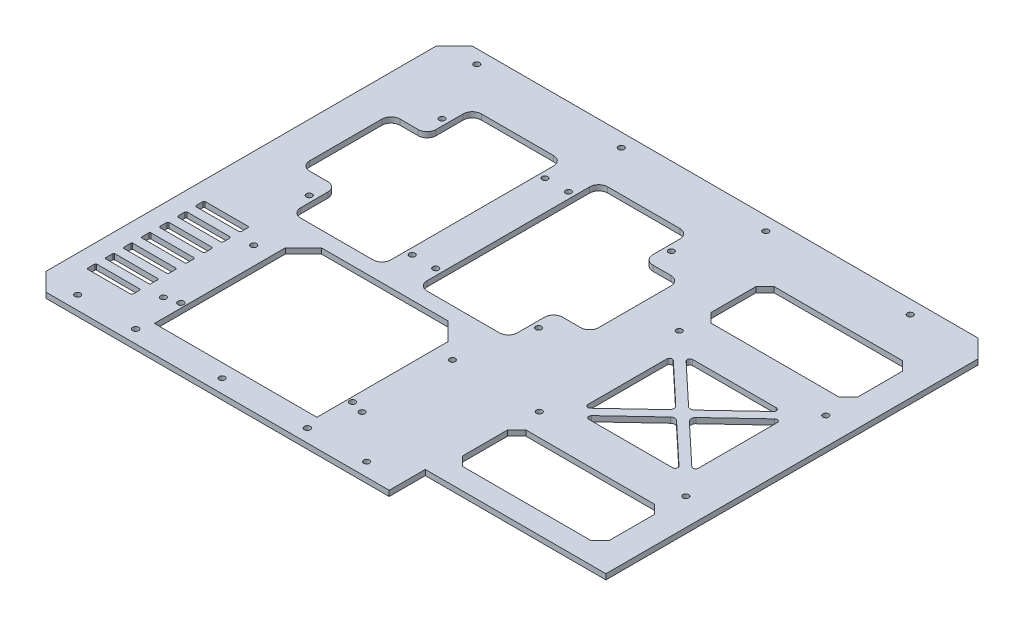
SolidWorks part; units mm, degrees
material "Thornel Mat VMA"
ref_plane "前视基准面" through (0, 0, 0) normal (0, 0, 1) x (1, 0, 0)
ref_plane "上视基准面" through (0, 0, 0) normal (0, 1, 0) x (1, 0, 0)
ref_plane "右视基准面" through (0, 0, 0) normal (1, 0, 0) x (0, 0, -1)
sketch "草图1" plane through (0, 0, 0) normal (0, 1, 0) x (1, 0, 0)
  line L0 (-100, -110.5) -> (100, -110.5) construction
  line L1 (-100, -118) -> (100, -118)
  line L2 (-100, -118) -> (-100, 118)
  line L3 (-100, 118) -> (100, 118)
  line L4 (100, -118) -> (100, 118)
  line L5 (-100, -118) -> (100, 118) construction
  line L6 (-100, 118) -> (100, -118) construction
  line L7 (0, 0) -> (61.3463, 0) construction
  line L8 (0, 0) -> (0, -52.9296) construction
  circle A0 centre (0, -110.5) radius 1.6
  circle A1 centre (-80, -110.5) radius 1.6
  circle A2 centre (80, -110.5) radius 1.6
  circle A3 centre (80, 110.5) radius 1.6
  circle A4 centre (0, 110.5) radius 1.6
  circle A5 centre (-80, 110.5) radius 1.6
  point P0 (0, 0)
  dimension "D4" = 3.2
  dimension "D6" = 3.2
  dimension "D1" = 200
  dimension "D2" = 236
  dimension "D3" = 7.5
  dimension "D5" = 80
extrude "凸台-拉伸1" add sketch "草图1" along normal blind 3
sketch "草图2" plane through (0, 3, 0) normal (0, 1, 0) x (1, 0, 0)
  line L0 (0, -110.5) -> (0, 110.5) construction
  line L1 (100, 118) -> (-100, 118) construction
  line L2 (6.5, 74.75) -> (63.5, 74.75) construction
  line L3 (6.5, 74.75) -> (6.5, 1.25) construction
  line L4 (6.5, 1.25) -> (63.5, 1.25) construction
  line L5 (63.5, 74.75) -> (63.5, 1.25) construction
  line L6 (6.5, 74.75) -> (63.5, 1.25) construction
  line L7 (6.5, 1.25) -> (63.5, 74.75) construction
  circle A0 centre (6.5, 74.75) radius 1.6
  circle A1 centre (63.5, 74.75) radius 1.6
  circle A2 centre (6.5, 1.25) radius 1.6
  circle A3 centre (63.5, 1.25) radius 1.6
  circle A4 centre (-6.5, 74.75) radius 1.6
  circle A5 centre (-63.5, 74.75) radius 1.6
  circle A6 centre (-63.5, 1.25) radius 1.6
  circle A7 centre (-6.5, 1.25) radius 1.6
  point P4 (35, 38)
  dimension "D5" = 3.2
  dimension "D6" = 3.2
  dimension "D7" = 3.2
  dimension "D8" = 3.2
  dimension "D1" = 73.5
  dimension "D2" = 57
  dimension "D3" = 35
  dimension "D4" = 80
extrude "切除-拉伸1" cut sketch "草图2" against normal up to next
sketch "草图3" plane through (0, 3, 0) normal (0, 1, 0) x (1, 0, 0)
  line L0 (-63.5, 1.25) -> (-6.5, 1.25) construction
  line L1 (-63.5, 74.75) -> (-6.5, 74.75) construction
  line L2 (-35, 74.75) -> (-35, 1.25) construction
  line L3 (0, 0) -> (0, 32.6506) construction
  line L4 (-60, -12) -> (-10, -12)
  line L5 (-60, -12) -> (-60, 88)
  line L6 (-60, 88) -> (-10, 88)
  line L7 (-10, -12) -> (-10, 88)
  line L8 (-60, -12) -> (-10, 88) construction
  line L9 (-60, 88) -> (-10, -12) construction
  line L10 (60, -12) -> (10, -12)
  line L11 (10, -12) -> (10, 88)
  line L12 (60, 88) -> (10, 88)
  line L13 (60, -12) -> (60, 88)
  point P10 (-35, 38)
  dimension "D1" = 50
  dimension "D2" = 100
extrude "切除-拉伸2" cut sketch "草图3" against normal up to next
sketch "草图4" plane through (0, 3, 0) normal (0, 1, 0) x (1, 0, 0)
  line L0 (-60, 38) -> (-70, 38) construction
  line L1 (-60, 88) -> (-60, -12) construction
  line L2 (0, 0) -> (0, 48.7718) construction
  line L3 (-80, 13) -> (-60, 13)
  line L4 (-80, 13) -> (-80, 63)
  line L5 (-80, 63) -> (-60, 63)
  line L6 (-60, 13) -> (-60, 63)
  line L7 (-80, 13) -> (-60, 63) construction
  line L8 (-80, 63) -> (-60, 13) construction
  line L9 (80, 13) -> (60, 13)
  line L10 (60, 13) -> (60, 63)
  line L11 (80, 63) -> (60, 63)
  line L12 (80, 13) -> (80, 63)
  dimension "D1" = 10
  dimension "D2" = 50
extrude "切除-拉伸3" cut sketch "草图4" against normal up to next
fillet "圆角1" radius 5 16 edges at (10, 1.5, 12) (60, 1.5, 12) (60, 1.5, -13) (80, 1.5, -13) (80, 1.5, -63) (60, 1.5, -63) (60, 1.5, -88) (10, 1.5, -88) (-60, 1.5, -13) (-80, 1.5, -13) (-80, 1.5, -63) (-60, 1.5, -63) (-10, 1.5, -88) (-60, 1.5, -88) (-10, 1.5, 12) (-60, 1.5, 12)
sketch "草图5" plane through (0, 3, 0) normal (0, 1, 0) x (1, 0, 0)
  line L0 (0, -110.5) -> (0, -65.5) construction
  line L2 (-25, -40.5) -> (25, -40.5) construction
  line L3 (-25, -40.5) -> (-25, -90.5) construction
  line L4 (-25, -90.5) -> (25, -90.5) construction
  line L5 (25, -40.5) -> (25, -90.5) construction
  line L6 (-25, -40.5) -> (25, -90.5) construction
  line L7 (-25, -90.5) -> (25, -40.5) construction
  circle A0 centre (25, -40.5) radius 1.6
  circle A1 centre (-25, -40.5) radius 1.6
  circle A2 centre (25, -90.5) radius 1.6
  circle A3 centre (-25, -90.5) radius 1.6
  dimension "D4" = 3.2
  dimension "D5" = 3.2
  dimension "D6" = 3.2
  dimension "D7" = 3.2
  dimension "D1" = 45
  dimension "D2" = 50
  dimension "D3" = 50
extrude "切除-拉伸4" cut sketch "草图5" against normal up to next
sketch "草图6" plane through (0, 3, 0) normal (0, 1, 0) x (1, 0, 0)
  line L0 (-25, -40.5) -> (0, -65.5) construction
  line L1 (-22.5, -52.5711) -> (-22.5, -78.4289)
  line L2 (-18.2322, -80.1967) -> (-5.3033, -67.2678)
  line L3 (-18.2322, -50.8033) -> (-5.3033, -63.7322)
  line L4 (-25, -40.5) -> (-25, -90.5) construction
  line L5 (-25, -90.5) -> (0, -65.5) construction
  line L6 (-22.5, -46.5355) -> (-3.5355, -65.5) construction
  line L7 (-22.5, -84.4645) -> (-3.5355, -65.5) construction
  line L8 (-22.5, -46.5355) -> (-22.5, -84.4645) construction
  line L9 (12.9289, -43) -> (-12.9289, -43)
  line L10 (14.6967, -47.2678) -> (1.7678, -60.1967)
  line L11 (-14.6967, -47.2678) -> (-1.7678, -60.1967)
  line L12 (22.5, -78.4289) -> (22.5, -52.5711)
  line L13 (18.2322, -80.1967) -> (5.3033, -67.2678)
  line L14 (18.2322, -50.8033) -> (5.3033, -63.7322)
  line L15 (-12.9289, -88) -> (12.9289, -88)
  line L16 (-14.6967, -83.7322) -> (-1.7678, -70.8033)
  line L17 (14.6967, -83.7322) -> (1.7678, -70.8033)
  arc A0 (-5.3033, -63.7322) -> (-5.3033, -67.2678) centre (-7.0711, -65.5) cw
  arc A1 (-18.2322, -80.1967) -> (-22.5, -78.4289) centre (-20, -78.4289) cw
  arc A2 (-18.2322, -50.8033) -> (-22.5, -52.5711) centre (-20, -52.5711) ccw
  arc A3 (-14.6967, -47.2678) -> (-12.9289, -43) centre (-12.9289, -45.5) cw
  arc A4 (14.6967, -47.2678) -> (12.9289, -43) centre (12.9289, -45.5) ccw
  arc A5 (1.7678, -60.1967) -> (-1.7678, -60.1967) centre (0, -58.4289) cw
  arc A6 (18.2322, -50.8033) -> (22.5, -52.5711) centre (20, -52.5711) cw
  arc A7 (18.2322, -80.1967) -> (22.5, -78.4289) centre (20, -78.4289) ccw
  arc A8 (5.3033, -67.2678) -> (5.3033, -63.7322) centre (7.0711, -65.5) cw
  arc A9 (14.6967, -83.7322) -> (12.9289, -88) centre (12.9289, -85.5) cw
  arc A10 (-14.6967, -83.7322) -> (-12.9289, -88) centre (-12.9289, -85.5) ccw
  arc A11 (-1.7678, -70.8033) -> (1.7678, -70.8033) centre (0, -72.5711) cw
  point P47 (0, -65.5)
  dimension "D2" = 2.5
  dimension "D1" = 2.5
  dimension "D3" = 4
extrude "切除-拉伸5" cut sketch "草图6" against normal up to next
sketch "草图7" plane through (0, 3, 0) normal (0, 1, 0) x (1, 0, 0)
  line L0 (-22.5, -65.5) -> (22.5, -65.5) construction
  line L1 (-22.5, -52.5711) -> (-22.5, -78.4289) construction
  line L2 (22.5, -78.4289) -> (22.5, -52.5711) construction
  line L3 (-100, -118) -> (100, -118) construction
  line L4 (-35, -28) -> (35, -28)
  line L5 (-35, -28) -> (-35, -103)
  line L6 (-35, -103) -> (35, -103)
  line L7 (35, -28) -> (35, -103)
  line L8 (-35, -28) -> (35, -103) construction
  line L9 (-35, -103) -> (35, -28) construction
  point P6 (0, -65.5)
  dimension "D1" = 70
  dimension "D2" = 15
extrude "切除-拉伸6" cut sketch "草图7" against normal up to next
sketch "草图8" plane through (0, 3, 0) normal (0, 1, 0) x (1, 0, 0)
  line L0 (35, -28) -> (-35, -28) construction
  line L1 (-35, -20.5) -> (35, -20.5)
  line L2 (-35, -20.5) -> (-35, -35.5)
  line L3 (-35, -35.5) -> (35, -35.5)
  line L4 (35, -20.5) -> (35, -35.5)
  line L5 (-35, -20.5) -> (35, -35.5) construction
  line L6 (-35, -35.5) -> (35, -20.5) construction
  line L7 (35, -103) -> (35, -28) construction
  point P0 (0, -28)
  dimension "D1" = 15
extrude "切除-拉伸7" cut sketch "草图8" against normal up to next
sketch "草图9" plane through (0, 3, 0) normal (0, 1, 0) x (1, 0, 0)
  line L0 (-35, -61.75) -> (35, -61.75) construction
  line L1 (-35, -20.5) -> (-35, -103) construction
  line L2 (35, -103) -> (35, -20.5) construction
  line L4 (-45, -20.5) -> (45, -20.5)
  line L5 (-45, -20.5) -> (-45, -103)
  line L6 (-45, -103) -> (45, -103)
  line L7 (45, -20.5) -> (45, -103)
  line L8 (-45, -20.5) -> (45, -103) construction
  line L9 (-45, -103) -> (45, -20.5) construction
  point P6 (0, -61.75)
  dimension "D1" = 82.5
  dimension "D2" = 90
extrude "切除-拉伸8" cut sketch "草图9" against normal up to next
chamfer "倒角2" distance 10 angle 45 2 edges at (45, 1.5, 20.5) (-45, 1.5, 20.5)
sketch "草图10" plane through (0, 3, 0) normal (0, 1, 0) x (1, 0, 0)
  line L0 (0, -118) -> (0, -88) construction
  line L1 (-100, -118) -> (100, -118) construction
  line L2 (-55, -88) -> (55, -88) construction
  line L3 (55, -88) -> (55, -38) construction
  circle A0 centre (55, -38) radius 1.6
  circle A1 centre (55, -88) radius 1.6
  circle A2 centre (-55, -88) radius 1.6
  circle A3 centre (-55, -38) radius 1.6
  dimension "D4" = 3.2
  dimension "D5" = 3.2
  dimension "D1" = 30
  dimension "D2" = 110
  dimension "D3" = 50
extrude "切除-拉伸9" cut sketch "草图10" against normal up to next
sketch "草图11" plane through (0, 3, 0) normal (0, 1, 0) x (1, 0, 0)
  line L0 (-55, -38) -> (-55, -88) construction
  line L1 (-55, -63) -> (-100, -63) construction
  line L2 (-100, 118) -> (-100, -118) construction
  line L3 (-89.5, -60.5) -> (-90, -61)
  line L4 (-89.5, -60.5) -> (-65.5, -60.5)
  line L5 (-90, -61) -> (-90, -65)
  line L6 (-89.5, -65.5) -> (-65.5, -65.5)
  line L7 (-65, -61) -> (-65, -65)
  line L8 (-90, -60.5) -> (-65, -65.5) construction
  line L9 (-90, -65.5) -> (-65, -60.5) construction
  line L10 (-65.5, -60.5) -> (-65, -61)
  line L11 (-90, -65) -> (-89.5, -65.5)
  line L12 (-65.5, -65.5) -> (-65, -65)
  line L13 (-90, -71) -> (-90, -75)
  line L14 (-89.5, -70.5) -> (-90, -71)
  line L15 (-89.5, -70.5) -> (-65.5, -70.5)
  line L16 (-65.5, -70.5) -> (-65, -71)
  line L17 (-65, -71) -> (-65, -75)
  line L18 (-65.5, -75.5) -> (-65, -75)
  line L19 (-89.5, -75.5) -> (-65.5, -75.5)
  line L20 (-90, -75) -> (-89.5, -75.5)
  line L21 (-90, -81) -> (-90, -85)
  line L22 (-89.5, -80.5) -> (-90, -81)
  line L23 (-89.5, -80.5) -> (-65.5, -80.5)
  line L24 (-65.5, -80.5) -> (-65, -81)
  line L25 (-65, -81) -> (-65, -85)
  line L26 (-65.5, -85.5) -> (-65, -85)
  line L27 (-89.5, -85.5) -> (-65.5, -85.5)
  line L28 (-90, -85) -> (-89.5, -85.5)
  line L29 (-90, -91) -> (-90, -95)
  line L30 (-89.5, -90.5) -> (-90, -91)
  line L31 (-89.5, -90.5) -> (-65.5, -90.5)
  line L32 (-65.5, -90.5) -> (-65, -91)
  line L33 (-65, -91) -> (-65, -95)
  line L34 (-65.5, -95.5) -> (-65, -95)
  line L35 (-89.5, -95.5) -> (-65.5, -95.5)
  line L36 (-90, -95) -> (-89.5, -95.5)
  line L37 (-90, -31) -> (-89.5, -30.5)
  line L38 (-89.5, -30.5) -> (-65.5, -30.5)
  line L39 (-65.5, -30.5) -> (-65, -31)
  line L40 (-65, -35) -> (-65, -31)
  line L41 (-65.5, -35.5) -> (-65, -35)
  line L42 (-89.5, -35.5) -> (-65.5, -35.5)
  line L43 (-89.5, -35.5) -> (-90, -35)
  line L44 (-90, -35) -> (-90, -31)
  line L45 (-90, -41) -> (-89.5, -40.5)
  line L46 (-89.5, -40.5) -> (-65.5, -40.5)
  line L47 (-65.5, -40.5) -> (-65, -41)
  line L48 (-65, -45) -> (-65, -41)
  line L49 (-65.5, -45.5) -> (-65, -45)
  line L50 (-89.5, -45.5) -> (-65.5, -45.5)
  line L51 (-89.5, -45.5) -> (-90, -45)
  line L52 (-90, -45) -> (-90, -41)
  line L53 (-90, -51) -> (-89.5, -50.5)
  line L54 (-89.5, -50.5) -> (-65.5, -50.5)
  line L55 (-65.5, -50.5) -> (-65, -51)
  line L56 (-65, -55) -> (-65, -51)
  line L57 (-65.5, -55.5) -> (-65, -55)
  line L58 (-89.5, -55.5) -> (-65.5, -55.5)
  line L59 (-89.5, -55.5) -> (-90, -55)
  line L60 (-90, -55) -> (-90, -51)
  line L61 (0, -118) -> (0, -57.7135) construction
  line L62 (-100, -118) -> (100, -118) construction
  point P8 (-77.5, -63)
  dimension "D1" = 25
  dimension "D2" = 5
  dimension "D3" = 4
extrude "切除-拉伸10" cut sketch "草图11" against normal up to next
sketch "草图12" plane through (100, 0, 0) normal (1, 0, 0) x (0, 0, -1)
  line L4 (-118, 0) -> (118, 0)
  line L5 (118, 0) -> (118, 3)
  line L6 (118, 3) -> (-118, 3)
  line L7 (-118, 3) -> (-118, 0)
  line L8 (-118, 0) -> (118, 0)
  line L9 (118, 0) -> (118, 3)
  line L10 (118, 3) -> (-118, 3)
  line L11 (-118, 3) -> (-118, 0)
  dimension "D1" = 0
extrude "凸台-拉伸2" add sketch "草图12" along normal blind 100
sketch "草图13" plane through (200, 0, 0) normal (1, 0, 0) x (0, 0, -1)
  line L0 (-118, 3) -> (-118, 0)
  line L1 (-118, 0) -> (-98, 0)
  line L2 (-118, 0) -> (118, 0) construction
  line L3 (-98, 0) -> (-98, 3)
  line L4 (118, 3) -> (-118, 3) construction
  line L5 (-98, 3) -> (-118, 3)
  dimension "D1" = 20
extrude "切除-拉伸11" cut sketch "草图13" against normal blind 100
sketch "草图14" plane through (0, 3, 0) normal (0, 1, 0) x (1, 0, 0)
  line L0 (-100, 0) -> (200, 0) construction
  line L1 (-100, 118) -> (-100, -118) construction
  line L2 (200, 118) -> (200, -98) construction
  line L4 (103.85, 38.735) -> (185, 38.735) construction
  line L5 (103.85, 38.735) -> (103.85, -38.735) construction
  line L6 (103.85, -38.735) -> (185, -38.735) construction
  line L7 (185, 38.735) -> (185, -38.735) construction
  line L8 (103.85, 38.735) -> (185, -38.735) construction
  line L9 (103.85, -38.735) -> (185, 38.735) construction
  circle A0 centre (103.85, 38.735) radius 1.6
  circle A1 centre (185, 38.735) radius 1.6
  circle A2 centre (103.85, -38.735) radius 1.6
  circle A3 centre (185, -38.735) radius 1.6
  point P7 (144.425, 0)
  dimension "D4" = 3.2
  dimension "D5" = 3.2
  dimension "D6" = 3.2
  dimension "D7" = 3.2
  dimension "D1" = 81.15
  dimension "D2" = 77.47
  dimension "D3" = 15
extrude "切除-拉伸12" cut sketch "草图14" against normal up to next
sketch "草图15" plane through (0, 3, 0) normal (0, 1, 0) x (1, 0, 0)
  line L0 (103.85, 38.735) -> (185, 38.735) construction
  line L1 (185, 38.735) -> (185, -38.735) construction
  line L2 (185, -38.735) -> (103.85, -38.735) construction
  line L3 (103.85, -38.735) -> (103.85, 38.735) construction
  line L4 (113.85, -28.735) -> (113.85, 28.735)
  line L5 (113.85, 28.735) -> (175, 28.735)
  line L6 (175, 28.735) -> (175, -28.735)
  line L7 (175, -28.735) -> (113.85, -28.735)
  dimension "D1" = 10
extrude "切除-拉伸13" cut sketch "草图15" against normal up to next
sketch "草图16" plane through (0, 3, 0) normal (0, 1, 0) x (1, 0, 0)
  line L0 (113.85, 28.735) -> (175, -28.735)
  line L1 (113.85, -28.735) -> (175, 28.735)
extrude "拉伸-薄壁1" add sketch "草图16" against normal up to surface (3 mm away) thin up to face at (144.425, 0, 0) thin type mid plane wall 5
fillet "圆角2" radius 1.5 8 edges at (171.3495, 1.5, 28.735) (175, 1.5, 25.3042) (175, 1.5, -25.3042) (171.3495, 1.5, -28.735) (117.5005, 1.5, -28.735) (113.85, 1.5, -25.3042) (113.85, 1.5, 25.3042) (117.5005, 1.5, 28.735)
fillet "圆角3" radius 2.5 4 edges at (144.425, 1.5, 3.4308) (148.0755, 1.5, 0) (144.425, 1.5, -3.4308) (140.7745, 1.5, 0)
sketch "草图17" plane through (0, 3, 0) normal (0, 1, 0) x (1, 0, 0)
  line L0 (103.85, -38.735) -> (185, -38.735) construction
  line L1 (144.425, -38.735) -> (144.425, -68.735) construction
  line L2 (200, 118) -> (200, -98) construction
  line L3 (103.85, -51.235) -> (185, -51.235)
  line L4 (103.85, -51.235) -> (103.85, -86.235)
  line L5 (103.85, -86.235) -> (185, -86.235)
  line L6 (185, -51.235) -> (185, -86.235)
  line L7 (103.85, -51.235) -> (185, -86.235) construction
  line L8 (103.85, -86.235) -> (185, -51.235) construction
  line L9 (137.124, 0) -> (153.9236, 0) construction
  line L10 (103.85, 86.235) -> (185, 86.235)
  line L11 (185, 51.235) -> (185, 86.235)
  line L12 (103.85, 51.235) -> (103.85, 86.235)
  line L13 (103.85, 51.235) -> (185, 51.235)
  dimension "D1" = 15
  dimension "D2" = 30
  dimension "D3" = 35
extrude "切除-拉伸14" cut sketch "草图17" against normal up to next
chamfer "倒角3" distance 5 angle 45 8 edges at (185, 1.5, -51.235) (103.85, 1.5, -51.235) (103.85, 1.5, -86.235) (185, 1.5, -86.235) (103.85, 1.5, 86.235) (103.85, 1.5, 51.235) (185, 1.5, 51.235) (185, 1.5, 86.235)
sketch "草图18" plane through (0, 0, 0) normal (0, -1, 0) x (1, 0, 0)
  line L0 (80, -110.5) -> (160, -110.5) construction
  circle A0 centre (160, -110.5) radius 1.6
  dimension "D2" = 3.2
  dimension "D1" = 80
extrude "切除-拉伸15" cut sketch "草图18" against normal up to next
chamfer "倒角4" distance 10 angle 45 3 edges at (-100, 1.5, 118) (-100, 1.5, -118) (200, 1.5, -118)
sketch "草图19" plane through (0, 3, 0) normal (0, 1, 0) x (1, 0, 0)
  line L0 (44.7179, -98) -> (76.9112, -120.542)
  line L1 (-44.5228, -98) -> (44.7179, -98)
  line L3 (-76.7162, -120.542) -> (76.9112, -120.542)
  line L8 (100, -98) -> (200, -98) construction
  line L9 (-44.5228, -98) -> (-76.7162, -120.542)
  dimension "D1" = 35
  dimension "D2" = 0
  dimension "D5" = 35
sketch "草图20" plane through (0, 0, 0) normal (0, -1, 0) x (1, 0, 0)
  circle A0 centre (-47.5, 85.8263) radius 1.65
  circle A1 centre (-47.5, 110.8263) radius 1.65
  circle A2 centre (47.5, 85.8263) radius 1.65
  circle A3 centre (47.5, 110.8263) radius 1.65
extrude "切除-拉伸16" cut sketch "草图20" against normal blind 10
